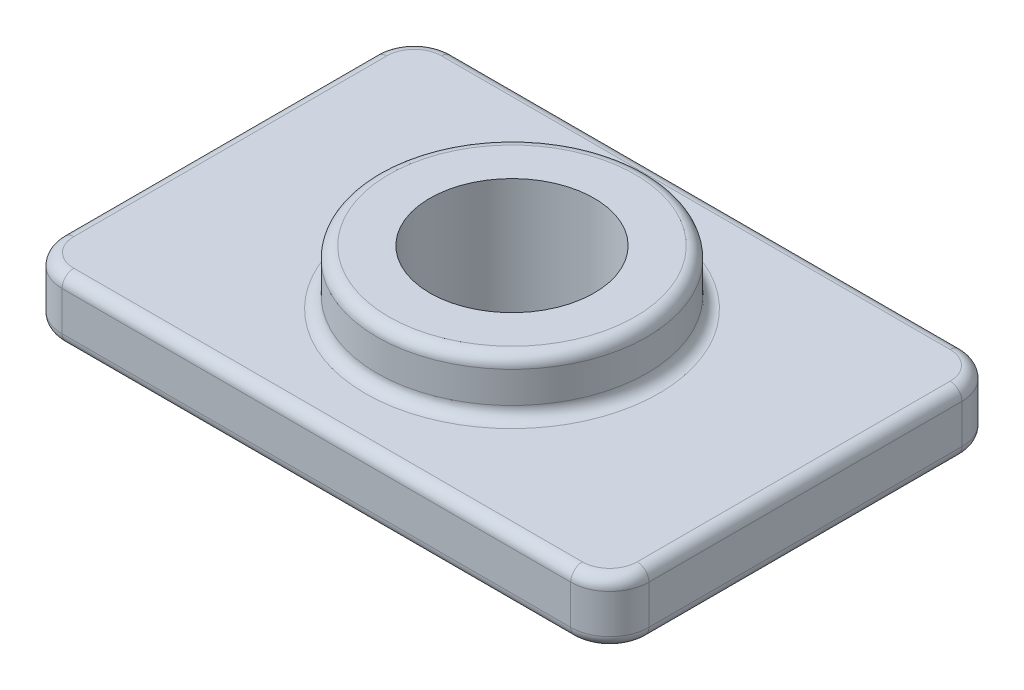
SolidWorks part; units mm, degrees
material "Plain Carbon Steel"
ref_plane "Front Plane" through (0, 0, 0) normal (0, 0, 1) x (1, 0, 0)
ref_plane "Top Plane" through (0, 0, 0) normal (0, 1, 0) x (1, 0, 0)
ref_plane "Right Plane" through (0, 0, 0) normal (1, 0, 0) x (0, 0, -1)
sketch "Sketch1" plane through (0, 0, 0) normal (0, 1, 0) x (1, 0, 0)
  line L0 (0, 1) -> (0, 0) construction
  line L1 (1, 0) -> (14, 0)
  line L2 (0, 1) -> (0, 9)
  line L3 (1, 10) -> (14, 10)
  line L4 (15, 1) -> (15, 9)
  line L5 (0, 0) -> (1, 0) construction
  arc A0 (1, 10) -> (0, 9) centre (1, 9) ccw
  arc A1 (15, 9) -> (14, 10) centre (14, 9) ccw
  arc A2 (14, 0) -> (15, 1) centre (14, 1) ccw
  arc A3 (0, 1) -> (1, 0) centre (1, 1) ccw
  dimension "D3" = 2
  dimension "D1" = 10
  dimension "D2" = 15
extrude "Boss-Extrude1" add sketch "Sketch1" along normal blind 1.6
sketch "Sketch2" plane through (0, 1.6, 0) normal (0, 1, 0) x (1, 0, 0)
  line L0 (7.5, 10) -> (7.5, 0) construction
  line L1 (14, 10) -> (1, 10) construction
  line L2 (1, 0) -> (14, 0) construction
  circle A0 centre (7.5, 5) radius 3.45
  dimension "D1" = 6.9
extrude "Boss-Extrude2" add sketch "Sketch2" along normal blind 1.4
hole_wizard "Tap Drill for M5x0.8 Tap1" positions "3DSketch1" profile "Sketch4" hole size "M5x0.8" standard "ANSI Metric" end condition through all
sketch3d "3DSketch1"
  line L0 (7.5, 3, -5) -> (7.5, 1.6, -5) construction
  point P0 (7.5, 3, -5)
sketch "Sketch4" plane through (7.5, 3, -5) normal (1, 0, 0) x (0, 0, 1)
  line L0 (0, 0) -> (0, 3)
  line L1 (0, 3) -> (2.1, 3)
  line L2 (2.1, 3) -> (2.1, 0)
  line L5 (2.1, 0) -> (0, 0)
  line L11 (0, -6.35) -> (0, 107.95) construction
  dimension "Thru Hole Dia." = 4.2
  dimension "Thru Hole Depth" = 3
fillet "Fillet2" radius 0.3 18 edges at (0.2929, 1.6, -9.7071) (7.5, 1.6, -10) (14.7071, 1.6, -9.7071) (15, 1.6, -5) (14.7071, 1.6, -0.2929) (7.5, 1.6, 0) (0.2929, 1.6, -0.2929) (0.2929, 0, -9.7071) (7.5, 0, -10) (14.7071, 0, -9.7071) (15, 0, -5) (14.7071, 0, -0.2929) (7.5, 0, 0) (0.2929, 0, -0.2929) (7.5, 3, -1.55) (7.5, 1.6, -1.55) (0, 1.6, -5) (0, 0, -5)
